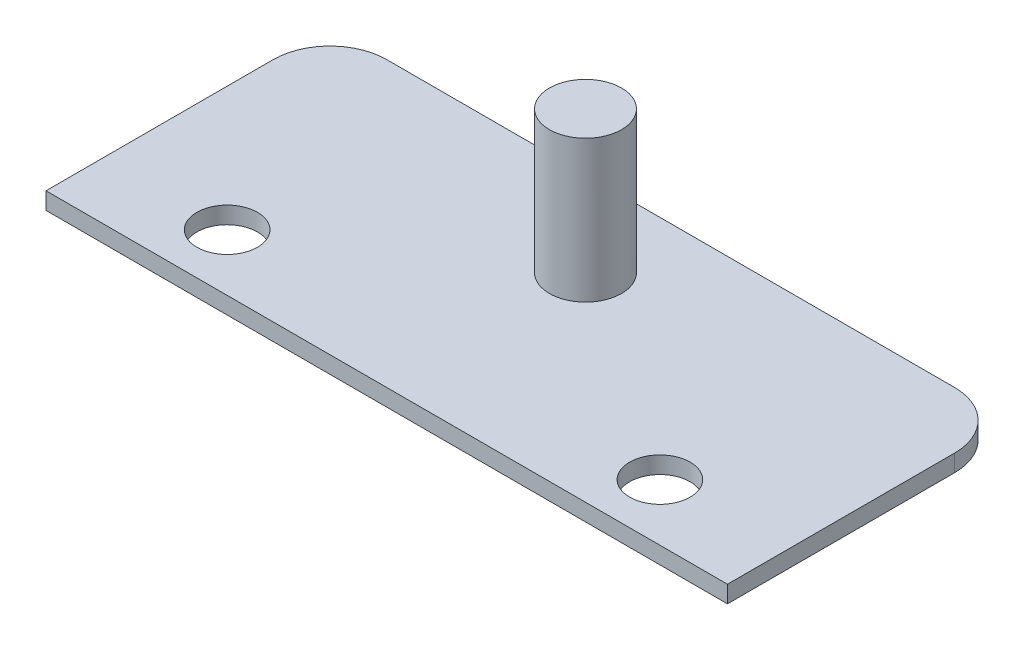
SolidWorks part; units mm, degrees
ref_plane "Front Plane" through (0, 0, 0) normal (0, 0, 1) x (1, 0, 0)
ref_plane "Top Plane" through (0, 0, 0) normal (0, 1, 0) x (1, 0, 0)
ref_plane "Right Plane" through (0, 0, 0) normal (1, 0, 0) x (0, 0, -1)
sketch "Sketch1" plane through (0, 0, 0) normal (0, 1, 0) x (1, 0, 0)
  line L1 (0, 0) -> (120, 0)
  line L2 (0, 0) -> (0, 50)
  line L3 (0, 50) -> (120, 50)
  line L4 (120, 0) -> (120, 50)
  dimension "D1" = 50
  dimension "D2" = 120
extrude "Boss-Extrude1" add sketch "Sketch1" along normal blind 3
sketch "Sketch2" plane through (0, 3, 0) normal (0, 1, 0) x (1, 0, 0)
  line L0 (60, 50) -> (60, 0) construction
  line L1 (120, 50) -> (0, 50) construction
  line L2 (0, 0) -> (120, 0) construction
  circle A0 centre (21.9, 10) radius 5.334
  circle A1 centre (98.1, 10) radius 5.334
  dimension "D1" = 10.668
  dimension "D2" = 76.2
  dimension "D3" = 10
extrude "Cut-Extrude1" cut sketch "Sketch2" against normal through all
sketch "Sketch3" plane through (0, 3, 0) normal (0, 1, 0) x (1, 0, 0)
  line L0 (60, 50) -> (60, 0) construction
  line L1 (120, 50) -> (0, 50) construction
  line L2 (0, 0) -> (120, 0) construction
  circle A0 centre (60, 35) radius 6.35
  dimension "D2" = 12.7
  dimension "D1" = 15
extrude "Boss-Extrude2" add sketch "Sketch3" along normal blind 25
fillet "Fillet1" radius 10 2 edges at (120, 1.5, -50) (0, 1.5, -50)
